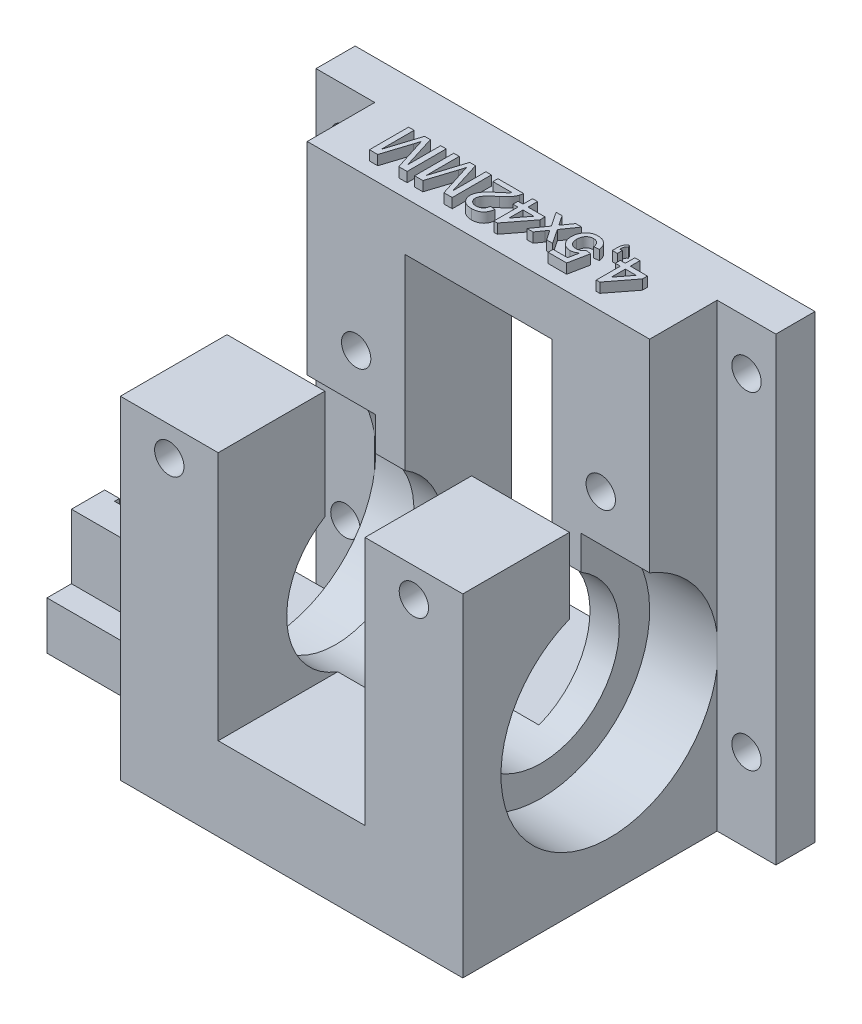
SolidWorks part; units mm, degrees
ref_plane "Спереди" through (0, 0, 0) normal (0, 0, 1) x (1, 0, 0)
ref_plane "Сверху" through (0, 0, 0) normal (0, 1, 0) x (1, 0, 0)
ref_plane "Справа" through (0, 0, 0) normal (1, 0, 0) x (0, 0, -1)
sketch "Эскиз1" plane through (0, 0, 0) normal (0, 1, 0) x (1, 0, 0)
  line L1 (17.5, -15) -> (-17.5, -15)
  line L2 (17.5, -15) -> (17.5, 15)
  line L3 (17.5, 15) -> (-17.5, 15)
  line L4 (-17.5, -15) -> (-17.5, 15)
  line L5 (17.5, -15) -> (-17.5, 15) construction
  line L6 (17.5, 15) -> (-17.5, -15) construction
  point P0 (0, 0)
  dimension "D1" = 35
  dimension "D2" = 30
extrude "Бобышка-Вытянуть1" add sketch "Эскиз1" along normal blind 42
sketch "Эскиз2" plane through (0, 42, 0) normal (0, 1, 0) x (1, 0, 0)
  line L0 (17.5, 15) -> (-17.5, 15) construction
  line L1 (7.5, -15) -> (-7.5, -15)
  line L2 (7.5, -15) -> (7.5, 15)
  line L3 (7.5, 15) -> (-7.5, 15)
  line L4 (-7.5, -15) -> (-7.5, 15)
  line L5 (7.5, -15) -> (-7.5, 15) construction
  line L6 (7.5, 15) -> (-7.5, -15) construction
  point P0 (0, 0)
  dimension "D1" = 10
  dimension "D2" = 15
extrude "Вырез-Вытянуть1" cut sketch "Эскиз2" against normal blind 33.5
sketch "Эскиз3" plane through (-17.5, 0, 0) normal (-1, 0, 0) x (0, 0, 1)
  line L0 (15, 16) -> (-15, 16) construction
  line L2 (15, 42) -> (15, 0) construction
  line L3 (-15, 42) -> (-15, 0) construction
  line L4 (-15, 0) -> (15, 0) construction
  circle A0 centre (0, 16) radius 11.1
  point P11 (0, 16)
  point P15 (0, 0)
  dimension "D1" = 22.2
  dimension "D2" = 16
extrude "Вырез-Вытянуть2" cut sketch "Эскиз3" against normal blind 7
sketch "Эскиз4" plane through (17.5, 0, 0) normal (1, 0, 0) x (0, 0, -1)
  line L0 (-15, 16) -> (15, 16) construction
  line L3 (-15, 42) -> (-15, 0) construction
  line L4 (15, 42) -> (15, 0) construction
  circle A0 centre (0, 16) radius 11.1
  dimension "D1" = 22.2
  dimension "D2" = 16
extrude "Вырез-Вытянуть3" cut sketch "Эскиз4" against normal blind 7
sketch "Эскиз5" plane through (-10.5, 0, 0) normal (-1, 0, 0) x (0, 0, 1)
  circle A0 centre (0, 16) radius 8
  dimension "D1" = 16
extrude "Вырез-Вытянуть4" cut sketch "Эскиз5" against normal through all
sketch "Эскиз6" plane through (0, 42, 0) normal (0, 1, 0) x (1, 0, 0)
  line L0 (17.5, -15) -> (17.5, 15) construction
  line L1 (-17.5, 4.1) -> (17.5, 4.1)
  line L2 (-17.5, 4.1) -> (-17.5, -4.1)
  line L3 (-17.5, -4.1) -> (17.5, -4.1)
  line L4 (17.5, 4.1) -> (17.5, -4.1)
  line L5 (-17.5, 4.1) -> (17.5, -4.1) construction
  line L6 (-17.5, -4.1) -> (17.5, 4.1) construction
  point P0 (0, 0)
  dimension "D1" = 8.2
extrude "Вырез-Вытянуть5" cut sketch "Эскиз6" against normal blind 20
sketch "Эскиз7" plane through (0, 0, -15) normal (0, 0, -1) x (-1, 0, 0)
  line L0 (-17.5, 31) -> (-7.5, 31) construction
  line L1 (-17.5, 42) -> (-17.5, 0) construction
  line L2 (-7.5, 8.5) -> (-7.5, 42) construction
  line L3 (7.5, 31) -> (17.5, 31) construction
  line L4 (7.5, 8.5) -> (7.5, 42) construction
  line L5 (17.5, 42) -> (17.5, 0) construction
  line L6 (-17.5, 42) -> (-7.5, 42) construction
  circle A0 centre (-12.5, 31) radius 1.5
  circle A1 centre (12.5, 31) radius 1.5
  point P12 (-12.5, 31)
  point P15 (-12.5, 42)
  dimension "D2" = 3
  dimension "D1" = 11
extrude "Вырез-Вытянуть6" cut sketch "Эскиз7" against normal through all
sketch "Эскиз9" plane through (-17.5, 0, 0) normal (1, 0, 0) x (0, 0, -1)
  line L0 (-15, 2.45) -> (15, 2.45) construction
  line L1 (-15, 42) -> (-15, 0) construction
  line L2 (15, 42) -> (15, 0) construction
  line L3 (0, 4.9) -> (0, 0) construction
  line L4 (-15, 0) -> (15, 0) construction
  line L6 (7.5, 0) -> (-7.5, 0)
  line L7 (7.5, 0) -> (7.5, 4.9)
  line L8 (7.5, 4.9) -> (-7.5, 4.9)
  line L9 (-7.5, 0) -> (-7.5, 4.9)
  line L10 (7.5, 0) -> (-7.5, 4.9) construction
  line L11 (7.5, 4.9) -> (-7.5, 0) construction
  circle A0 centre (0, 16) radius 11.1 construction
  point P13 (0, 2.45)
  point P14 (0, 2.45)
  point P15 (0, 2.45)
  dimension "D1" = 15
  dimension "D2" = 4.9
extrude "Бобышка-Вытянуть2" add sketch "Эскиз9" against normal blind 15
sketch "Эскиз10" plane through (0, 4.9, 0) normal (0, 1, 0) x (1, 0, 0)
  line L0 (-29.5, 7.5) -> (-29.5, -7.5) construction
  line L1 (-32.5, 7.5) -> (-17.5, 7.5) construction
  line L2 (-32.5, -7.5) -> (-17.5, -7.5) construction
  line L3 (-32.5, 7.5) -> (-32.5, -7.5) construction
  line L4 (-26.5, -5) -> (-32.5, -5)
  line L5 (-26.5, -5) -> (-26.5, 5)
  line L6 (-26.5, 5) -> (-32.5, 5)
  line L7 (-32.5, -5) -> (-32.5, 5)
  line L8 (-26.5, -5) -> (-32.5, 5) construction
  line L9 (-26.5, 5) -> (-32.5, -5) construction
  point P6 (-29.5, 0)
  point P13 (-32.5, 0)
  dimension "D1" = 10
  dimension "D2" = 3
extrude "Бобышка-Вытянуть3" add sketch "Эскиз10" along normal blind 6.6
sketch "Эскиз11" plane through (0, 11.5, 0) normal (0, 1, 0) x (1, 0, 0)
  line L0 (-26.5, 0) -> (-32.5, 0) construction
  line L1 (-26.5, -5) -> (-26.5, 5) construction
  line L2 (-32.5, 5) -> (-32.5, -5) construction
  line L3 (-31, 1.6) -> (-32.5, 1.6)
  line L4 (-31, -2.1) -> (-28, -2.1)
  line L5 (-31, 1.6) -> (-31, 2.1)
  line L6 (-31, 2.1) -> (-28, 2.1)
  line L7 (-28, -2.1) -> (-28, 2.1)
  line L8 (-31, -2.1) -> (-28, 2.1) construction
  line L9 (-31, 2.1) -> (-28, -2.1) construction
  line L10 (-32.5, 1.6) -> (-32.5, -1.6)
  line L11 (-32.5, -1.6) -> (-31, -1.6)
  line L12 (-31, -1.6) -> (-31, -2.1)
  point P6 (-29.5, 0)
  dimension "D1" = 4.2
  dimension "D2" = 3
  dimension "D3" = 3.2
extrude "Вырез-Вытянуть8" cut sketch "Эскиз11" against normal blind 1.3
sketch "Эскиз12" plane through (-32.5, 0, 0) normal (-1, 0, 0) x (0, 0, 1)
  line L0 (0, 10.2) -> (0, 0) construction
  line L1 (-1.6, 10.2) -> (1.6, 10.2) construction
  line L2 (7.5, 0) -> (-7.5, 0) construction
  line L4 (1.6, 0) -> (-1.6, 0)
  line L5 (1.6, 0) -> (1.6, 10.2)
  line L6 (1.6, 10.2) -> (-1.6, 10.2)
  line L7 (-1.6, 0) -> (-1.6, 10.2)
  line L8 (1.6, 0) -> (-1.6, 10.2) construction
  line L9 (1.6, 10.2) -> (-1.6, 0) construction
  point P6 (0, 5.1)
extrude "Вырез-Вытянуть9" cut sketch "Эскиз12" against normal blind 1
sketch "Эскиз13" plane through (-17.5, 0, 0) normal (-1, 0, 0) x (0, 0, 1)
  line L0 (-11.1, 16) -> (11.1, 16) construction
  line L1 (0, 16) -> (0, 0) construction
  circle A0 centre (0, 16) radius 11.1 construction
  circle A1 centre (0, 16) radius 11.1 construction
  dimension "D1" = 16
sketch "Эскиз14" plane through (0, 42, 0) normal (0, 1, 0) x (1, 0, 0)
  line L0 (17.5, 9.55) -> (-17.5, 9.55) construction
  line L1 (17.5, 4.1) -> (17.5, 15) construction
  line L2 (-17.5, 15) -> (-17.5, 4.1) construction
  line L4 (-17.5, 15) -> (17.5, 15)
  line L5 (-17.5, 15) -> (-17.5, 4.1)
  line L6 (-17.5, 4.1) -> (17.5, 4.1)
  line L7 (17.5, 15) -> (17.5, 4.1)
  line L8 (-17.5, 15) -> (17.5, 4.1) construction
  line L9 (-17.5, 4.1) -> (17.5, 15) construction
  point P6 (0, 9.55)
extrude "Бобышка-Вытянуть4" add sketch "Эскиз14" along normal blind 5
sketch "Эскиз15" plane through (0, 42, 0) normal (0, 1, 0) x (1, 0, 0)
  line L0 (-7.5, -4.1) -> (-17.5, -15) construction
  line L1 (17.5, -4.1) -> (7.5, -15) construction
  line L3 (-17.5, -15) -> (-7.5, -15)
  line L4 (-17.5, -15) -> (-17.5, -4.1)
  line L5 (-17.5, -4.1) -> (-7.5, -4.1)
  line L6 (-7.5, -15) -> (-7.5, -4.1)
  line L7 (-17.5, -15) -> (-7.5, -4.1) construction
  line L8 (-17.5, -4.1) -> (-7.5, -15) construction
  line L9 (7.5, -15) -> (17.5, -15)
  line L10 (7.5, -15) -> (7.5, -4.1)
  line L11 (7.5, -4.1) -> (17.5, -4.1)
  line L12 (17.5, -15) -> (17.5, -4.1)
  line L13 (7.5, -15) -> (17.5, -4.1) construction
  line L14 (7.5, -4.1) -> (17.5, -15) construction
  point P8 (-12.5, -9.55)
  point P9 (12.5, -9.55)
extrude "Вырез-Вытянуть10" cut sketch "Эскиз15" against normal blind 8
sketch "Эскиз17" plane through (0, 47, 0) normal (0, 1, 0) x (1, 0, 0)
  line L0 (17.5, 9.55) -> (-17.5, 9.55) construction
  line L1 (17.5, 4.1) -> (17.5, 15) construction
  line L2 (-17.5, 15) -> (-17.5, 4.1) construction
  text T0 "4,5x42MM"
extrude "Бобышка-Вытянуть5" add sketch "Эскиз17" along normal blind 1
sketch "Эскиз23" plane through (17.5, 0, 0) normal (1, 0, 0) x (0, 0, -1)
  line L0 (13, 47) -> (13, 0) construction
  line L1 (4.1, 47) -> (15, 47) construction
  line L2 (-15, 0) -> (15, 0) construction
  line L4 (11, 0) -> (15, 0)
  line L5 (11, 0) -> (11, 47)
  line L6 (11, 47) -> (15, 47)
  line L7 (15, 0) -> (15, 47)
  line L8 (11, 0) -> (15, 47) construction
  line L9 (11, 47) -> (15, 0) construction
  point P6 (13, 23.5)
  dimension "D1" = 2
extrude "Бобышка-Вытянуть7" add sketch "Эскиз23" along normal blind 6
sketch "Эскиз25" plane through (-17.5, 0, 0) normal (-1, 0, 0) x (0, 0, 1)
  line L0 (-13, 47) -> (-13, 0) construction
  line L1 (-15, 47) -> (-4.1, 47) construction
  line L2 (-15, 0) -> (-7.5, 0) construction
  line L4 (-11, 0) -> (-15, 0)
  line L5 (-11, 0) -> (-11, 47)
  line L6 (-11, 47) -> (-15, 47)
  line L7 (-15, 0) -> (-15, 47)
  line L8 (-11, 0) -> (-15, 47) construction
  line L9 (-11, 47) -> (-15, 0) construction
  point P6 (-13, 23.5)
  dimension "D1" = 2
extrude "Бобышка-Вытянуть8" add sketch "Эскиз25" along normal blind 6
sketch "Эскиз26" plane through (0, 0, -15) normal (0, 0, -1) x (-1, 0, 0)
  line L0 (-20.5, 42) -> (-20.5, 8.5) construction
  line L1 (-7.5, 42) -> (7.5, 42) construction
  line L2 (23.5, 47) -> (23.5, 0) construction
  line L5 (-20.5, 8.5) -> (20.5, 8.5) construction
  line L6 (20.5, 8.5) -> (20.5, 42) construction
  line L7 (20.5, 42) -> (-20.5, 42) construction
  circle A0 centre (-20.5, 42) radius 1.5
  circle A1 centre (-20.5, 8.5) radius 1.5
  circle A2 centre (20.5, 42) radius 1.5
  circle A3 centre (20.5, 8.5) radius 1.5
  point P4 (0, 42)
  point P7 (0, 42)
  dimension "D3" = 3
  dimension "D1" = 3
  dimension "D4" = 41
extrude "Вырез-Вытянуть12" cut sketch "Эскиз26" against normal through all
sketch "Эскиз27" plane through (0, 0, -15) normal (0, 0, -1) x (-1, 0, 0)
  circle A0 centre (12.5, 31) radius 3
  circle A1 centre (-12.5, 31) radius 3
  dimension "D1" = 6
extrude "Вырез-Вытянуть13" cut sketch "Эскиз27" against normal blind 3
